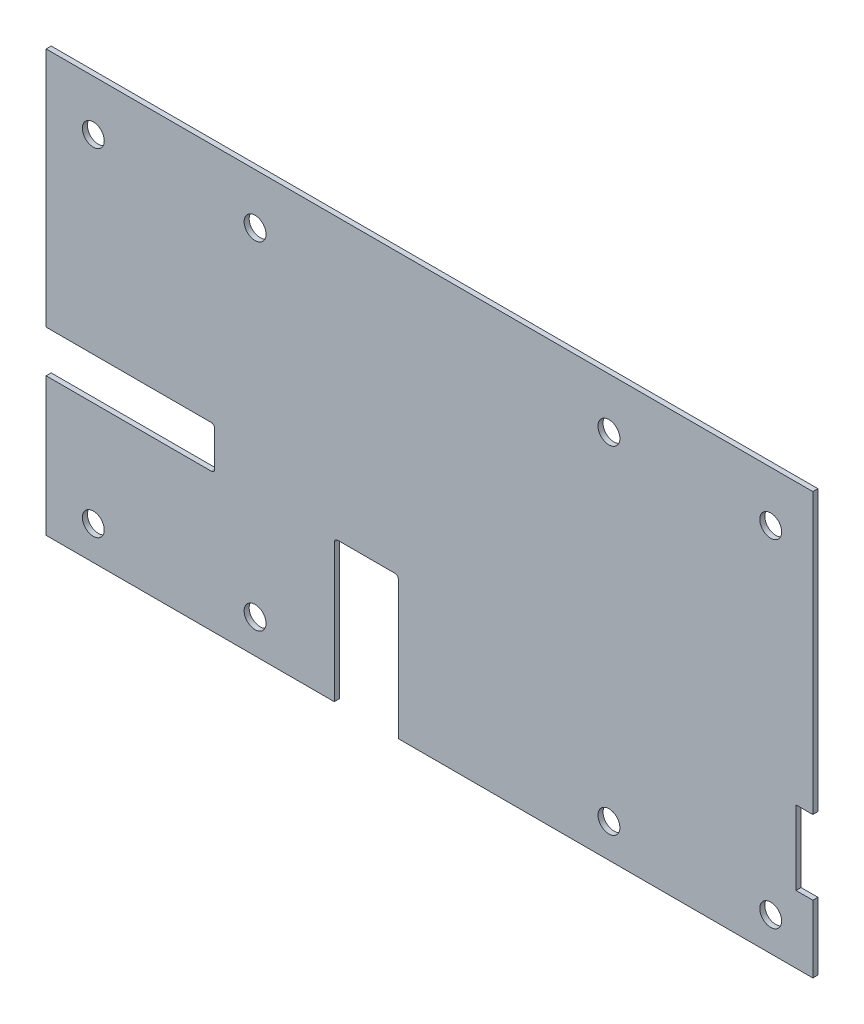
SolidWorks part; units mm, degrees
ref_plane "Plan de face" through (0, 0, 0) normal (0, 0, 1) x (1, 0, 0)
ref_plane "Plan de dessus" through (0, 0, 0) normal (0, 1, 0) x (1, 0, 0)
ref_plane "Plan de droite" through (0, 0, 0) normal (1, 0, 0) x (0, 0, -1)
sketch "Esquisse1" plane through (0, 0, 0) normal (0, 0, 1) x (1, 0, 0)
  line L1 (227.5, -125) -> (-227.5, -125)
  line L2 (227.5, -125) -> (227.5, 125)
  line L3 (227.5, 125) -> (-227.5, 125)
  line L4 (-227.5, -125) -> (-227.5, 125)
  line L5 (227.5, -125) -> (-227.5, 125) construction
  line L6 (227.5, 125) -> (-227.5, -125) construction
  line L7 (-199.5, 95) -> (-103.5, 95) construction
  line L8 (-199.5, 95) -> (-199.5, -105) construction
  line L9 (-199.5, -105) -> (-103.5, -105) construction
  line L10 (-103.5, 95) -> (-103.5, -105) construction
  line L11 (106.5, 95) -> (202.5, 95) construction
  line L12 (106.5, 95) -> (106.5, -105) construction
  line L13 (106.5, -105) -> (202.5, -105) construction
  line L14 (202.5, 95) -> (202.5, -105) construction
  circle A0 centre (106.5, 95) radius 6.5
  circle A1 centre (202.5, 95) radius 6.5
  circle A2 centre (106.5, -105) radius 6.5
  circle A3 centre (202.5, -105) radius 6.5
  circle A4 centre (-103.5, -105) radius 6.5
  circle A5 centre (-103.5, 95) radius 6.5
  circle A6 centre (-199.5, 95) radius 6.5
  circle A7 centre (-199.5, -105) radius 6.5
  point P0 (0, 0)
  dimension "D11" = 13
  dimension "D1" = 455
  dimension "D2" = 250
  dimension "D3" = 96
  dimension "D4" = 96
  dimension "D5" = 200
  dimension "D6" = 20
  dimension "D7" = 0
  dimension "D8" = 402
  dimension "D9" = 25
  dimension "D10" = 0
extrude "Boss.-Extru.1" add sketch "Esquisse1" along normal blind 3
sketch "Esquisse2" plane through (0, 0, 3) normal (0, 0, 1) x (1, 0, 0)
  line L0 (227.5, 125) -> (-227.5, 125) construction
  line L1 (-227.5, 125) -> (-127.5, 125)
  line L2 (-227.5, 125) -> (-227.5, 122)
  line L3 (-227.5, 122) -> (-127.5, 122)
  line L4 (-127.5, 125) -> (-127.5, 122)
  line L5 (-100, 125) -> (100, 125)
  line L6 (-100, 125) -> (-100, 122)
  line L7 (-100, 122) -> (100, 122)
  line L8 (100, 125) -> (100, 122)
  line L9 (227.5, -125) -> (227.5, 125) construction
  line L10 (227.5, 125) -> (127.545, 125)
  line L12 (224.5, 122) -> (127.545, 122)
  line L13 (127.545, 125) -> (127.545, 122)
  line L14 (227.5, -125) -> (224.5, -125)
  line L15 (227.5, -125) -> (227.5, -50)
  line L16 (227.5, -50) -> (224.5, -50)
  line L17 (224.5, -125) -> (224.5, -50)
  line L18 (227.5, 40) -> (224.5, 40)
  line L19 (227.5, 40) -> (227.5, 125)
  line L21 (224.5, 40) -> (224.5, 122)
  point P16 (0, 122)
  dimension "D1" = 100
  dimension "D2" = 100
  dimension "D3" = 3
  dimension "D4" = 0
  dimension "D5" = 200
  dimension "D6" = 3
  dimension "D7" = 75
  dimension "D8" = 85
extrude "Enlèv. mat.-Extru.1" [suppressed] cut sketch "Esquisse2" against normal blind 10
sketch "Esquisse3" [suppressed] plane through (0, 0, 3) normal (0, 0, 1) x (1, 0, 0)
  line L0 (274.5, 122) -> (274.5, 40) construction
  line L1 (-75.5, 122) -> (-72.5, 122)
  line L2 (-75.5, 122) -> (-75.5, 40)
  line L3 (-75.5, 40) -> (-72.5, 40)
  line L4 (-72.5, 122) -> (-72.5, 40)
  line L5 (-100, 122) -> (100, 122) construction
  line L7 (-277.5, -125) -> (274.5, -125) construction
  line L8 (-75.5, -125) -> (-72.5, -125)
  line L9 (-75.5, -125) -> (-75.5, -50)
  line L10 (-75.5, -50) -> (-72.5, -50)
  line L11 (-72.5, -125) -> (-72.5, -50)
  dimension "D1" = 3
  dimension "D2" = 350
  dimension "D3" = 0
  dimension "D4" = 82
  dimension "D5" = 75
  dimension "D6" = 0
extrude "Enlèv. mat.-Extru.2" [suppressed] cut sketch "Esquisse3" against normal blind 3
mirror "Symétrie1" [suppressed] about plane through (0, 0, 0) normal (1, 0, 0)
sketch "Esquisse4" plane through (0, 0, 3) normal (0, 0, 1) x (1, 0, 0)
  line L0 (-227.5, 125) -> (-227.5, -125) construction
  line L1 (-227.5, -43) -> (-127.5, -43)
  line L2 (-227.5, -43) -> (-227.5, -18)
  line L3 (-227.5, -18) -> (-127.5, -18)
  line L4 (-127.5, -43) -> (-127.5, -18)
  line L5 (-52.5, -546.3015) -> (-52.5, -83) construction
  line L6 (-18.5, -41) -> (-56.5, -41)
  line L7 (-18.5, -41) -> (-18.5, -125)
  line L8 (-18.5, -125) -> (-56.5, -125)
  line L9 (-56.5, -41) -> (-56.5, -125)
  line L10 (-22.5, -546.3015) -> (-22.5, -83) construction
  line L11 (-227.5, -125) -> (227.5, -125) construction
  line L12 (1292.5, -43) -> (-227.5, -43) construction
  line L13 (-224.5, -43) -> (-227.5, -43) construction
  line L14 (227.5, -125) -> (227.5, 125) construction
  line L15 (227.5, -41) -> (217.5, -41)
  line L16 (227.5, -41) -> (227.5, -85)
  line L17 (227.5, -85) -> (217.5, -85)
  line L18 (217.5, -41) -> (217.5, -85)
  dimension "D1" = 4
  dimension "D2" = 4
  dimension "D3" = 0
  dimension "D4" = 25
  dimension "D5" = 100
  dimension "D6" = 2
  dimension "D7" = 10
  dimension "D8" = 44
extrude "Enlèv. mat.-Extru.3" cut sketch "Esquisse4" against normal blind 10
sketch "Esquisse6" [suppressed] plane through (0, 0, 3) normal (0, 0, 1) x (1, 0, 0)
  line L1 (-274.5, -50) -> (-277.5, -50)
  line L2 (-274.5, -50) -> (-274.5, -45)
  line L3 (-274.5, -45) -> (-277.5, -45)
  line L4 (-277.5, -50) -> (-277.5, -45)
extrude "Enlèv. mat.-Extru.4" [suppressed] cut sketch "Esquisse6" against normal blind 10
fillet "Congé1" radius 2 4 edges at (-18.5, -41, 1.5) (-56.5, -41, 1.5) (-127.5, -43, 1.5) (-127.5, -18, 1.5)
